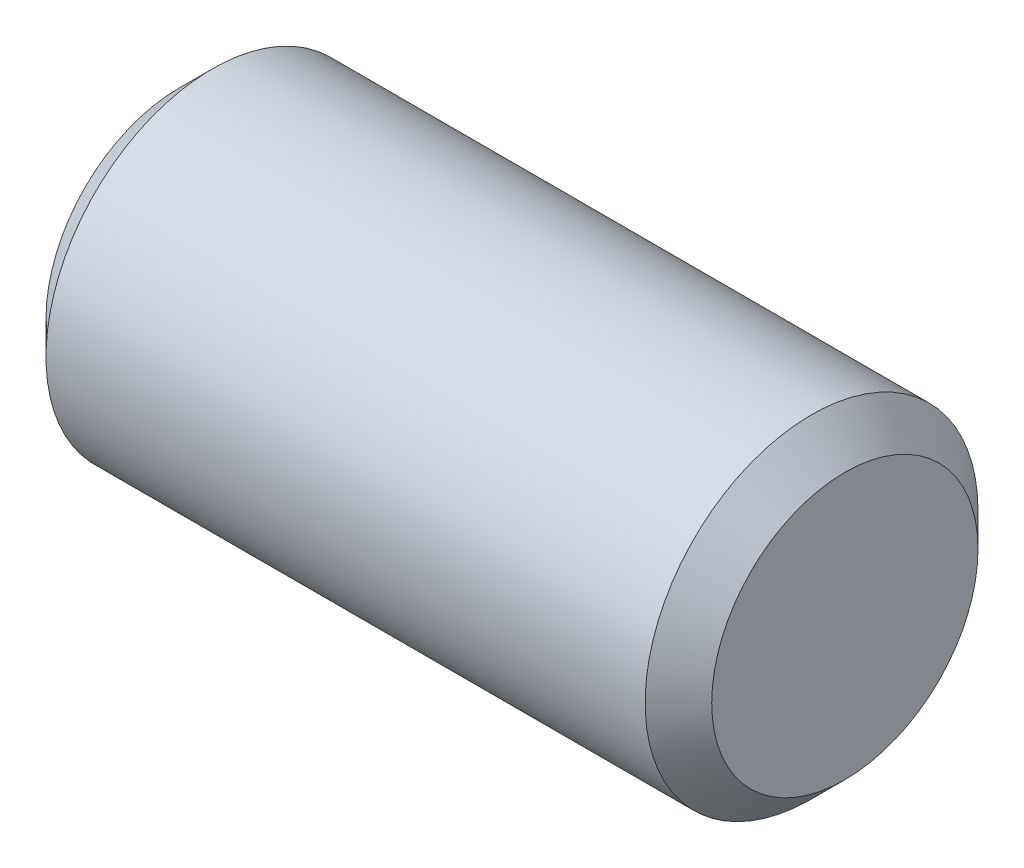
SolidWorks part; units mm, degrees
material "AISI 304"
ref_plane "Front" through (0, 0, 0) normal (0, 0, 1) x (1, 0, 0)
ref_plane "Top" through (0, 0, 0) normal (0, 1, 0) x (1, 0, 0)
ref_plane "Right" through (0, 0, 0) normal (1, 0, 0) x (0, 0, -1)
sketch "Sketch1" plane through (0, 0, 0) normal (0, 0, 1) x (1, 0, 0)
  line L0 (-6.35, 0) -> (6.35, 0) construction
  line L1 (6.35, 3.175) -> (6.35, -3.175) construction
  line L2 (-6.35, 3.175) -> (-6.35, -3.175) construction
  dimension "Length" = 12.7
  dimension "Diameter" = 6.35
sketch "Sketch2" plane through (0, 0, 0) normal (1, 0, 0) x (0, 0, -1)
  circle A0 centre (0, 0) radius 3.175
extrude "Extrude1" add sketch "Sketch2" against normal up to vertex (6.35 mm away) and the other way up to vertex (6.35 mm away) up to point (-6.35, 3.175, 0) other way up to point (6.35, 3.175, 0)
chamfer "Chamfer1" distance 0.635 angle 45 2 edges at (6.35, 0, -3.175) (-6.35, 0, -3.175)
equation "\"D1@Chamfer1\" = \"Diameter@Sketch1\"*.1"
